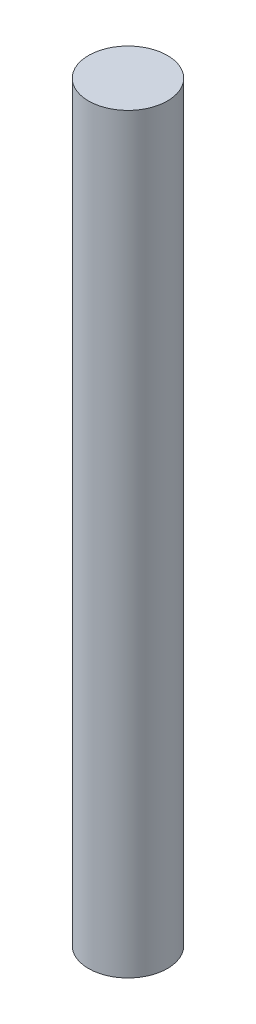
SolidWorks part; units mm, degrees
ref_plane "Front Plane" through (0, 0, 0) normal (0, 0, 1) x (1, 0, 0)
ref_plane "Top Plane" through (0, 0, 0) normal (0, 1, 0) x (1, 0, 0)
ref_plane "Right Plane" through (0, 0, 0) normal (1, 0, 0) x (0, 0, -1)
sketch "Sketch1" plane through (0, 0, 0) normal (0, 1, 0) x (1, 0, 0)
  circle A0 centre (0, 0) radius 2
extrude "Boss-Extrude1" add sketch "Sketch1" along normal blind 38.1
